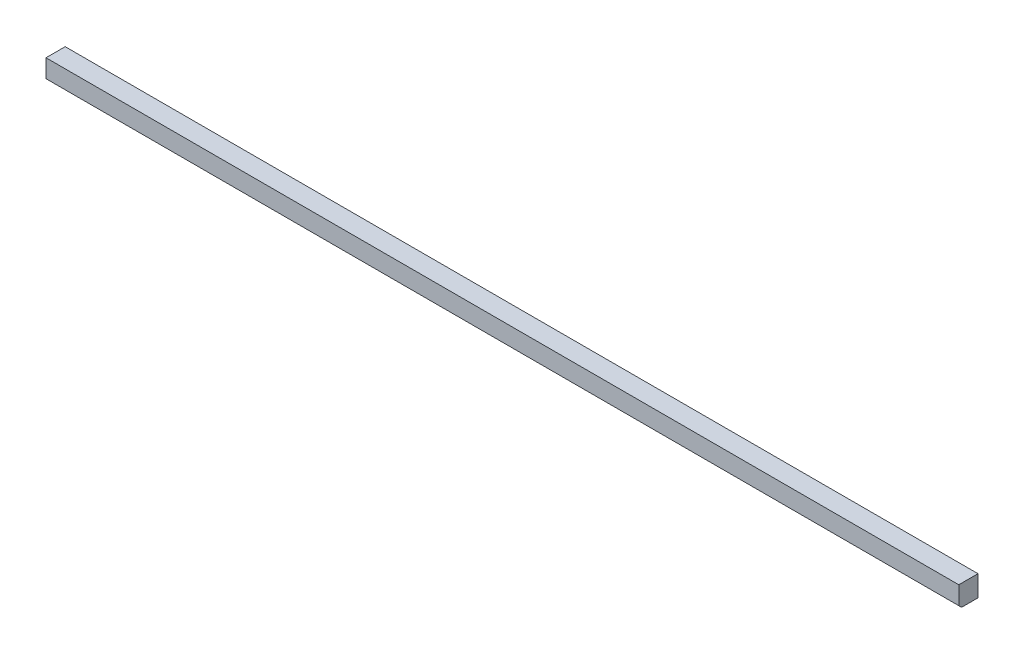
SolidWorks part; units mm, degrees
material "Oak"
ref_plane "Front Plane" through (0, 0, 0) normal (0, 0, 1) x (1, 0, 0)
ref_plane "Top Plane" through (0, 0, 0) normal (0, 1, 0) x (1, 0, 0)
ref_plane "Right Plane" through (0, 0, 0) normal (1, 0, 0) x (0, 0, -1)
sketch "Sketch1" plane through (0, 0, 0) normal (0, 1, 0) x (1, 0, 0)
  line L1 (0, 0) -> (830.2752, 0)
  line L2 (0, 0) -> (0, 17.4625)
  line L3 (0, 17.4625) -> (830.2752, 17.4625)
  line L4 (830.2752, 0) -> (830.2752, 17.4625)
  dimension "D1" = 17.4625
  dimension "D2" = 830.2752
extrude "Boss-Extrude1" add sketch "Sketch1" along normal blind 19.05
chamfer "Chamfer1" distance 2.54 angle 45 1 edges at (415.1376, 0, 0)
